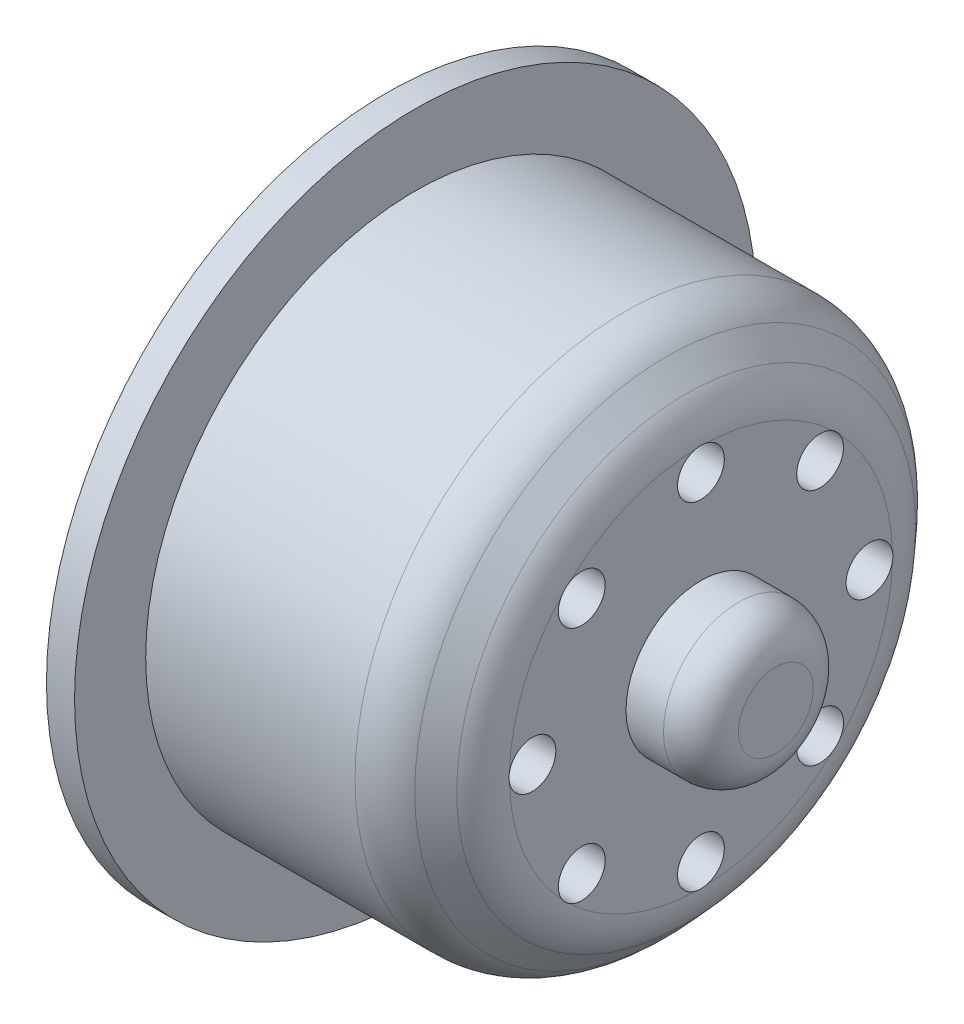
SolidWorks part; units mm, degrees
ref_plane "Front Plane" through (0, 0, 0) normal (0, 0, 1) x (1, 0, 0)
ref_plane "Top Plane" through (0, 0, 0) normal (0, 1, 0) x (1, 0, 0)
ref_plane "Right Plane" through (0, 0, 0) normal (1, 0, 0) x (0, 0, -1)
sketch "Sketch1" plane through (0, 0, 0) normal (0, 1, 0) x (1, 0, 0)
  line L0 (-12.3913, 0) -> (21, 0) construction
  line L1 (-4.6304, 14.4) -> (7.8696, 14.4)
  line L5 (13.3727, 0) -> (-6.1304, 0)
  line L8 (10.6196, 4) -> (14.6196, 4)
  line L9 (14.6196, 4) -> (14.6196, 0)
  line L10 (14.6196, 0) -> (13.3727, 0)
  line L11 (-4.6304, 14.4) -> (-4.6304, 18.2)
  line L12 (-4.6304, 18.2) -> (-6.1304, 18.2)
  line L13 (-6.1304, 18.2) -> (-6.1304, 0)
  line L15 (7.8696, 14.4) -> (10.6196, 11.3905)
  line L17 (10.6196, 11.3905) -> (10.6196, 4)
  dimension "D2" = 132.42
  dimension "D3" = 4.0767
  dimension "D4" = 12.5
  dimension "D5" = 28.8
  dimension "D6" = 3.0095
  dimension "D7" = 4
  dimension "D8" = 8
  dimension "D9" = 3.8
  dimension "D10" = 1.5
  dimension "D11" = 11.3905
revolve "Revolve1" add sketch "Sketch1" angle 360 about L0
fillet "Fillet1" radius 2 1 edges at (14.6196, 0, 4)
sketch "Sketch4" plane through (-6.1304, 0, 0) normal (-1, 0, 0) x (0, 0, 1)
  circle A0 centre (0, 0) radius 10.5
  dimension "D1" = 21
extrude "Cut-Extrude3" cut sketch "Sketch4" against normal blind 6
sketch "Sketch5" plane through (10.6196, 0, 0) normal (1, 0, 0) x (0, 0, -1)
  circle A0 centre (0, 0) radius 9 construction
  circle A1 centre (0, 9) radius 1.25
  circle A2 centre (6.364, 6.364) radius 1.25
  circle A3 centre (9, 0) radius 1.25
  circle A4 centre (6.364, -6.364) radius 1.25
  circle A5 centre (0, -9) radius 1.25
  circle A6 centre (-6.364, -6.364) radius 1.25
  circle A7 centre (-9, 0) radius 1.25
  circle A8 centre (-6.364, 6.364) radius 1.25
  point P22 (0, 0)
  dimension "D1" = 18
  dimension "D2" = 2.5
  dimension "D3" = 8
extrude "Cut-Extrude4" cut sketch "Sketch5" against normal up to surface (16.75 mm away) up to face at (-6.1304, 0, 10.5)
sketch "Sketch6" plane through (-6.1304, 0, 0) normal (-1, 0, 0) x (0, 0, 1)
  circle A0 centre (0, 0) radius 9 construction
  circle A1 centre (0, 9) radius 2.5
  circle A2 centre (6.364, 6.364) radius 2.5
  circle A3 centre (9, 0) radius 2.5
  circle A4 centre (6.364, -6.364) radius 2.5
  circle A5 centre (0, -9) radius 2.5
  circle A6 centre (-6.364, -6.364) radius 2.5
  circle A7 centre (-9, 0) radius 2.5
  circle A8 centre (-6.364, 6.364) radius 2.5
  point P22 (0, 0)
  dimension "D1" = 18
  dimension "D2" = 5
  dimension "D3" = 8
extrude "Cut-Extrude5" cut sketch "Sketch6" against normal offset from surface (11.75 mm away) 5 up to face at (10.6196, 9, -1.25)
fillet "Fillet2" radius 3 2 edges at (10.6196, 0, 11.3905) (7.8696, 0, 14.4)
